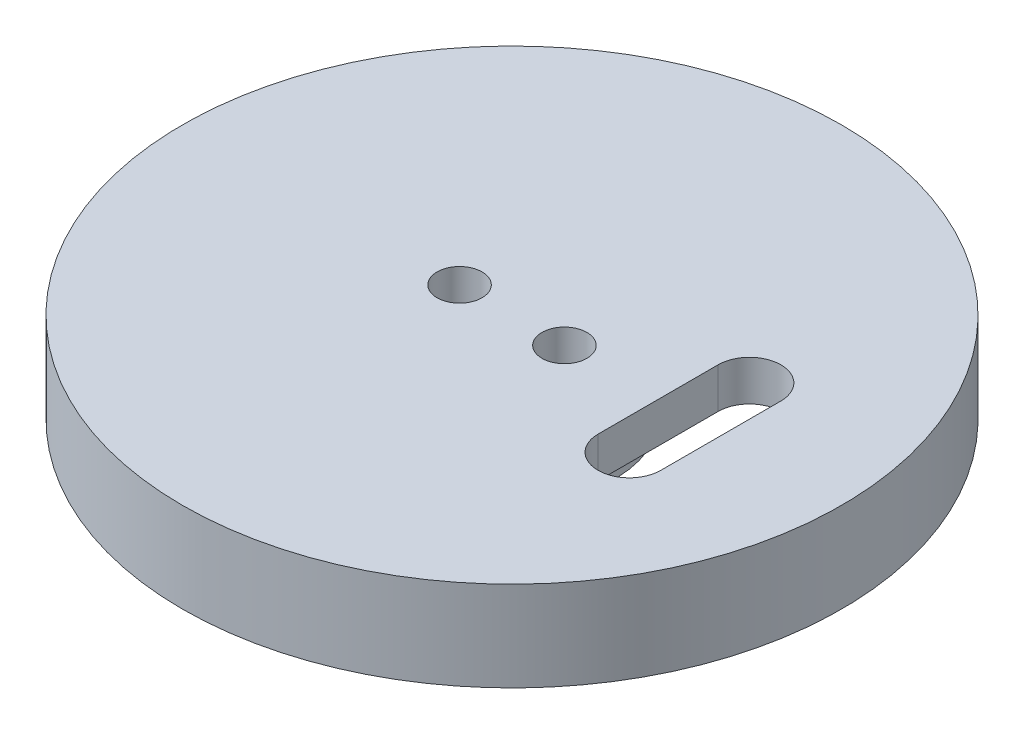
SolidWorks part; units mm, degrees
ref_plane "Plan de face" through (0, 0, 0) normal (0, 0, 1) x (1, 0, 0)
ref_plane "Plan de dessus" through (0, 0, 0) normal (0, 1, 0) x (1, 0, 0)
ref_plane "Plan de droite" through (0, 0, 0) normal (1, 0, 0) x (0, 0, -1)
sketch "Esquisse1" plane through (0, 0, 0) normal (0, 1, 0) x (1, 0, 0)
  line L0 (-3.5, 0) -> (3.5, 0) construction
  circle A0 centre (0, 0) radius 22
  circle A2 centre (-3.5, 0) radius 1.5
  circle A3 centre (3.5, 0) radius 1.5
  circle A15 centre (0, 0) radius 18 construction
  dimension "D1" = 44
  dimension "D2" = 36
  dimension "D3" = 3.5
  dimension "D4" = 7
  dimension "D5" = 3
  dimension "D6" = 3
extrude "Boss.-Extru.1" add sketch "Esquisse1" along normal blind 6
sketch "Esquisse2" plane through (0, 0, 0) normal (0, -1, 0) x (1, 0, 0)
  circle A0 centre (0, 0) radius 16.25
  circle A1 centre (0, 0) radius 6.9
  dimension "D1" = 32.5
  dimension "D2" = 13.8
extrude "Enlèv. mat.-Extru.1" cut sketch "Esquisse2" against normal blind 3.3
sketch "Esquisse3" plane through (0, 3.3, 0) normal (0, -1, 0) x (-1, 0, 0)
  line L0 (-11.8461, -4.0087) -> (-11.8461, 4.0087) construction
  line L1 (-13.9406, -4.0087) -> (-13.9406, 4.0087)
  line L2 (-9.7517, -4.0087) -> (-9.7517, 4.0087)
  line L3 (0, 0) -> (-15.8195, 0) construction
  arc A0 (-13.9406, -4.0087) -> (-9.7517, -4.0087) centre (-11.8461, -4.0087) ccw
  arc A1 (-9.7517, 4.0087) -> (-13.9406, 4.0087) centre (-11.8461, 4.0087) ccw
  point P2 (-11.8461, 0)
extrude "Enlèv. mat.-Extru.2" cut sketch "Esquisse3" against normal blind 3
